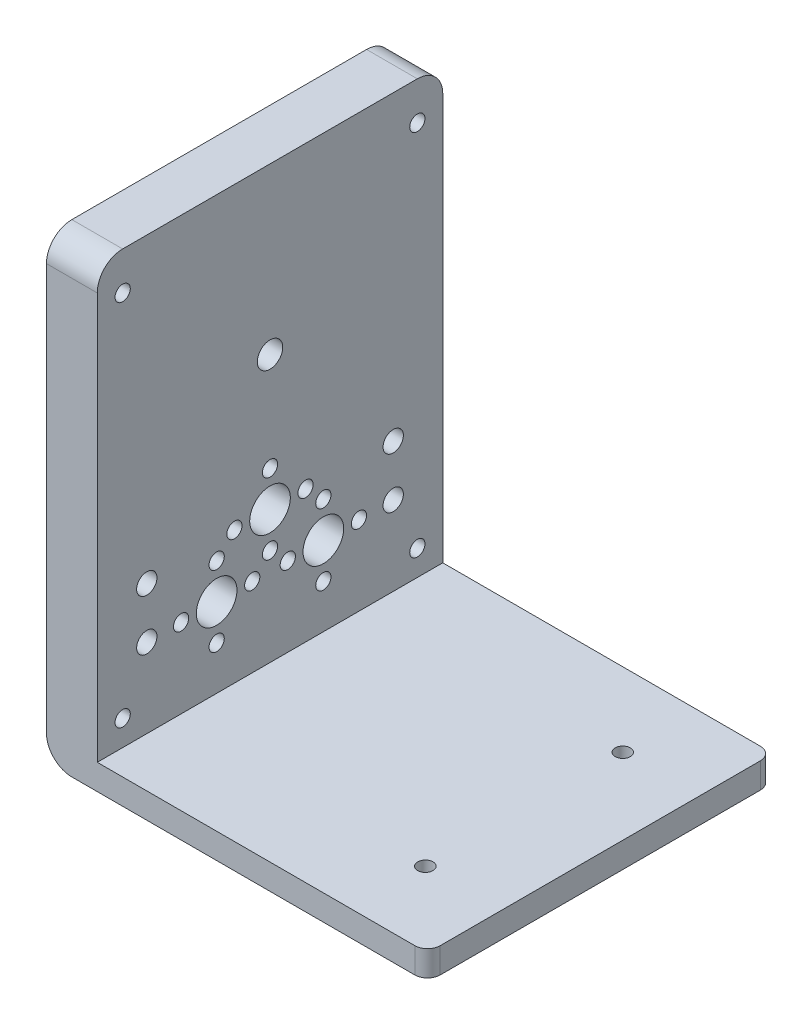
SolidWorks part; units mm, degrees
ref_plane "前视基准面" through (0, 0, 0) normal (0, 0, 1) x (1, 0, 0)
ref_plane "上视基准面" through (0, 0, 0) normal (0, 1, 0) x (1, 0, 0)
ref_plane "右视基准面" through (0, 0, 0) normal (1, 0, 0) x (0, 0, -1)
other "Configuration Table"
sketch "草图1" plane through (0, 0, 0) normal (0, 0, 1) x (1, 0, 0)
  line L0 (-15.419, 41.8994) -> (-15.419, -48.1006)
  line L1 (-15.419, -48.1006) -> (59.581, -48.1006)
  line L2 (59.581, -48.1006) -> (59.581, -43.1006)
  line L3 (59.581, -43.1006) -> (-5.419, -43.1006)
  line L4 (-5.419, -43.1006) -> (-5.419, 41.8994)
  line L5 (-5.419, 41.8994) -> (-15.419, 41.8994)
  dimension "D1" = 85
  dimension "D2" = 10
  dimension "D3" = 75
  dimension "D4" = 5
extrude "凸台-拉伸1" add sketch "草图1" along normal blind 68
sketch "草图2" plane through (-15.419, 0, 0) normal (-1, 0, 0) x (0, 0, 1)
  circle A0 centre (34, 9.3994) radius 2.5
extrude "切除-拉伸1" cut sketch "草图2" against normal through all
fillet "圆角1" radius 5 2 edges at (-10.419, 41.8994, 68) (-10.419, 41.8994, 0)
fillet "圆角3" radius 5 1 edges at (-15.419, -48.1006, 34)
sketch "草图7" plane through (-15.419, 0, 0) normal (-1, 0, 0) x (0, 0, 1)
  circle A2 centre (63, 34.3994) radius 1.5 construction
  circle A3 centre (5, 34.3994) radius 1.5 construction
  circle A4 centre (63, 34.3994) radius 1.5
  circle A5 centre (5, 34.3994) radius 1.5
extrude "切除-拉伸5" cut sketch "草图7" against normal blind 10
sketch "草图8" plane through (0, -48.1006, 0) normal (0, -1, 0) x (1, 0, 0)
  line L0 (-10.419, 68) -> (59.581, 0) construction
  line L1 (59.581, 68) -> (-10.419, 0) construction
  line L3 (59.581, 68) -> (59.581, 0) construction
  circle A1 centre (44.581, 14.5714) radius 1.5
  circle A2 centre (44.581, 53.4286) radius 1.5
  dimension "D6" = 3
  dimension "D7" = 3
  dimension "D2" = 15
  dimension "D3" = 15
extrude "切除-拉伸6" cut sketch "草图8" against normal blind 10
sketch "草图9" plane through (-15.419, 0, 0) normal (-1, 0, 0) x (0, 0, 1)
  line L0 (63, 36.8994) -> (63, -43.1006) construction
  line L1 (0, -43.1006) -> (68, -43.1006) construction
  line L2 (5, 36.8994) -> (5, -43.1006) construction
  line L3 (5, 36.8994) -> (5, 41.8994) construction
  circle A1 centre (5, -38.1006) radius 1.5
  circle A2 centre (63, -38.1006) radius 1.5
  dimension "D1" = 5
  dimension "D3" = 3
  dimension "D4" = 3
  dimension "D2" = 5
extrude "切除-拉伸7" cut sketch "草图9" against normal blind 10
fillet "圆角4" radius 2.5 2 edges at (59.581, -45.6006, 0) (59.581, -45.6006, 68)
sketch "草图14" plane through (-15.419, 0, 0) normal (-1, 0, 0) x (0, 0, 1)
  circle A1 centre (58.25, -27.4964) radius 2
  circle A2 centre (58.25, -27.4964) radius 2
  circle A3 centre (58.25, -17.4964) radius 2
  circle A4 centre (58.25, -17.4964) radius 2
  circle A5 centre (9.75, -17.4964) radius 2
  circle A6 centre (9.75, -17.4964) radius 2
  circle A7 centre (9.75, -27.4964) radius 2
  circle A8 centre (9.75, -27.4964) radius 2
  circle A9 centre (23.5, -34.4964) radius 1.5
  circle A10 centre (23.5, -34.4964) radius 1.5
  circle A11 centre (44.5, -27.4964) radius 4
  circle A12 centre (44.5, -27.4964) radius 4
  circle A13 centre (23.5, -27.4964) radius 4
  circle A14 centre (23.5, -27.4964) radius 4
  circle A15 centre (34, -16.9964) radius 4
  circle A20 centre (34, -16.9964) radius 4
  circle A21 centre (44.5, -20.4964) radius 1.5
  circle A22 centre (44.5, -20.4964) radius 1.5
  circle A23 centre (51.5, -27.4964) radius 1.5
  circle A24 centre (51.5, -27.4964) radius 1.5
  circle A25 centre (44.5, -34.4964) radius 1.5
  circle A26 centre (44.5, -34.4964) radius 1.5
  circle A27 centre (16.5, -27.4964) radius 1.5
  circle A28 centre (16.5, -27.4964) radius 1.5
  circle A29 centre (23.5, -20.4964) radius 1.5
  circle A30 centre (23.5, -20.4964) radius 1.5
  circle A31 centre (30.5, -27.4964) radius 1.5
  circle A32 centre (30.5, -27.4964) radius 1.5
  circle A33 centre (27, -16.9964) radius 1.5
  circle A34 centre (27, -16.9964) radius 1.5
  circle A35 centre (34, -9.9964) radius 1.5
  circle A36 centre (34, -9.9964) radius 1.5
  circle A37 centre (41, -16.9964) radius 1.5
  circle A38 centre (41, -16.9964) radius 1.5
  circle A39 centre (34, -23.9964) radius 1.5
  circle A40 centre (34, -23.9964) radius 1.5
  circle A41 centre (37.5, -27.4964) radius 1.5
  circle A42 centre (37.5, -27.4964) radius 1.5
  dimension "D1" = 0
  dimension "D2" = 0
  dimension "D3" = 0
  dimension "D4" = 0
  dimension "D5" = 0
  dimension "D6" = 0
  dimension "D7" = 0
  dimension "D9" = 0
  dimension "D10" = 0
  dimension "D11" = 0
  dimension "D12" = 0
  dimension "D13" = 0
  dimension "D14" = 0
  dimension "D15" = 0
  dimension "D16" = 0
  dimension "D17" = 0
  dimension "D18" = 0
  dimension "D19" = 0
  dimension "D20" = 0
extrude "切除-拉伸9" cut sketch "草图14" against normal through all
